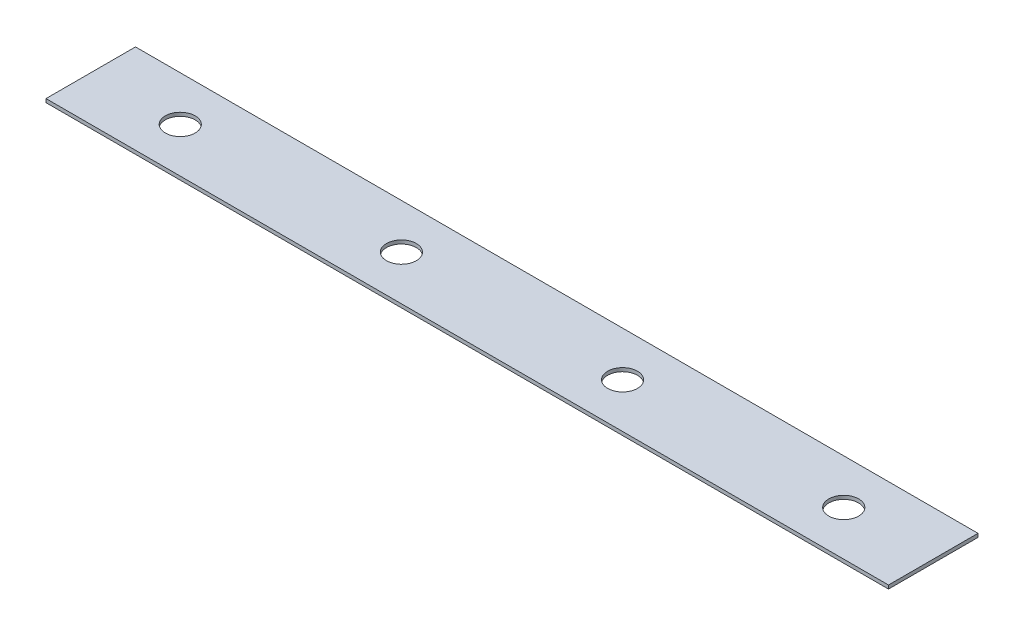
SolidWorks part; units mm, degrees
material "Plain Carbon Steel"
ref_plane "Front Plane" through (0, 0, 0) normal (0, 0, 1) x (1, 0, 0)
ref_plane "Top Plane" through (0, 0, 0) normal (0, 1, 0) x (1, 0, 0)
ref_plane "Right Plane" through (0, 0, 0) normal (1, 0, 0) x (0, 0, -1)
sketch "Sketch1" plane through (0, 0, 0) normal (1, 0, 0) x (0, 0, -1)
  line L1 (0, 0) -> (38.1, 0)
  line L2 (0, 0) -> (0, 1.5189)
  line L3 (0, 1.5189) -> (38.1, 1.5189)
  line L4 (38.1, 0) -> (38.1, 1.5189)
  dimension "D1" = 38.1
  dimension "D2" = 1.5189
extrude "Boss-Extrude1" add sketch "Sketch1" along normal blind 358.6378
sketch "Sketch2" plane through (0, 0, 0) normal (0, 0, 1) x (1, 0, 0)
  line L0 (0, 0) -> (358.6378, 0) construction
  point P4 (179.3189, 0)
sketch "Sketch3" plane through (0, 1.5189, 0) normal (0, 1, 0) x (1, 0, 0)
  line L0 (132.2459, 19.05) -> (38.1, 19.05) construction
  line L2 (132.2459, 19.05) -> (226.3919, 19.05) construction
  line L3 (226.3919, 19.05) -> (320.5378, 19.05) construction
  line L4 (320.5378, 19.05) -> (358.6378, 19.05) construction
  line L5 (358.6378, 38.1) -> (358.6378, 0) construction
  line L6 (38.1, 19.05) -> (0, 19.05) construction
  line L7 (0, 38.1) -> (0, 0) construction
  circle A0 centre (132.2459, 19.05) radius 6.35
  circle A1 centre (226.3919, 19.05) radius 6.35
  circle A2 centre (320.5378, 19.05) radius 6.35
  circle A3 centre (38.1, 19.05) radius 6.35
  dimension "D1" = 12.7
  dimension "D2" = 12.7
  dimension "D3" = 12.7
  dimension "D4" = 12.7
  dimension "D5" = 38.1
extrude "Cut-Extrude1" cut sketch "Sketch3" against normal through all
